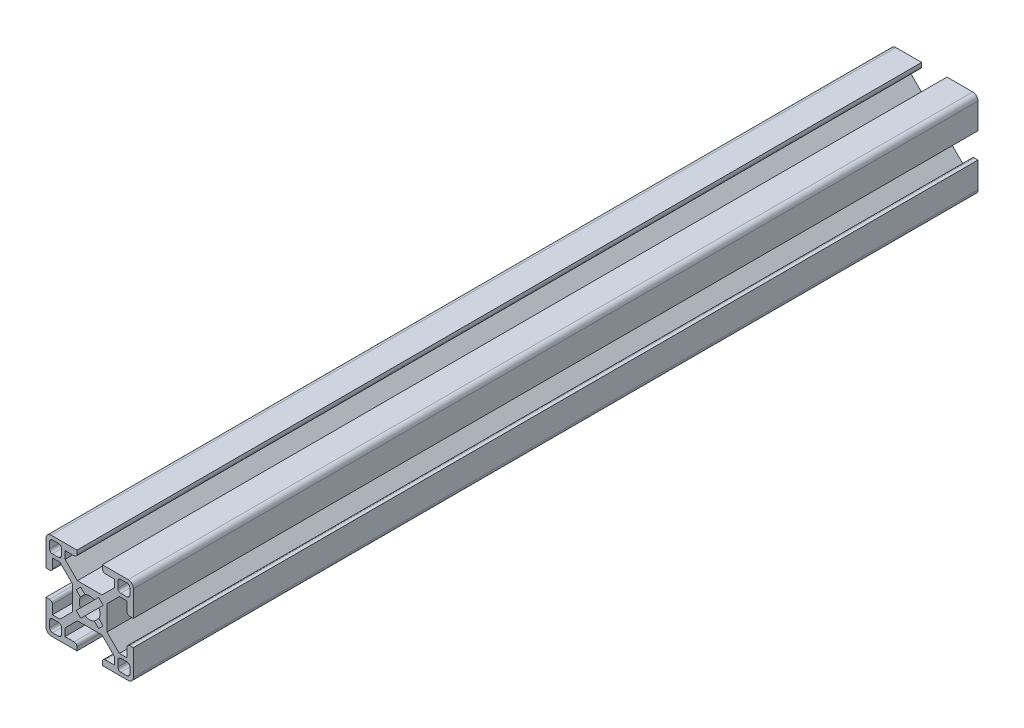
SolidWorks part; units mm, degrees
ref_plane "Front Plane" through (0, 0, 0) normal (0, 0, 1) x (1, 0, 0)
ref_plane "Top Plane" through (0, 0, 0) normal (0, 1, 0) x (1, 0, 0)
ref_plane "Right Plane" through (0, 0, 0) normal (1, 0, 0) x (0, 0, -1)
sketch "Sketch1" plane through (0, 0, 0) normal (0, 0, 1) x (1, 0, 0)
  line L0 (0, 0) -> (5.95, 0) construction
  line L1 (0, 0) -> (0, 5.95) construction
  line L2 (-5.95, 5.95) -> (5.95, 5.95)
  line L3 (5.95, 5.95) -> (5.95, 0)
  line L4 (4.2176, 5.95) -> (8.4602, 10.1926)
  line L5 (5.95, 5.95) -> (8.4425, 8.4425) construction
  line L6 (5.95, 4.2176) -> (10.1926, 8.4602)
  line L7 (8.4602, 12.7926) -> (8.4602, 8.4602)
  line L8 (8.4602, 8.4602) -> (12.7926, 8.4602)
  line L9 (12.7926, 8.4602) -> (12.7926, 5.3502)
  line L10 (13.7926, 4.3502) -> (14.9926, 4.3502)
  line L11 (14.9926, 4.3502) -> (14.9926, 13.1926)
  line L12 (8.4602, 8.4602) -> (14.9926, 14.9926) construction
  line L13 (4.3502, 13.7926) -> (4.3502, 14.9926)
  line L14 (4.3502, 14.9926) -> (13.1926, 14.9926)
  line L15 (5.3502, 12.7926) -> (8.4602, 12.7926)
  line L16 (-9.6602, 9.6602) -> (-13.7926, 13.7926) construction
  line L17 (10.6602, 13.7926) -> (12.7926, 13.7926)
  line L18 (9.6602, 12.7926) -> (9.6602, 10.6602)
  line L19 (10.6602, 9.6602) -> (12.7926, 9.6602)
  line L20 (13.7926, 12.7926) -> (13.7926, 10.6602)
  line L21 (9.6602, 13.7926) -> (13.7926, 9.6602) construction
  line L22 (9.6602, 9.6602) -> (13.7926, 13.7926) construction
  line L23 (-9.6602, 13.7926) -> (-13.7926, 9.6602) construction
  line L24 (-8.4602, 8.4602) -> (-14.9926, 14.9926) construction
  line L25 (-5.95, 5.95) -> (-8.4425, 8.4425) construction
  line L26 (-13.7926, 12.7926) -> (-13.7926, 10.6602)
  line L27 (-10.6602, 9.6602) -> (-12.7926, 9.6602)
  line L28 (-9.6602, 12.7926) -> (-9.6602, 10.6602)
  line L29 (-10.6602, 13.7926) -> (-12.7926, 13.7926)
  line L30 (-5.3502, 12.7926) -> (-8.4602, 12.7926)
  line L31 (-4.3502, 14.9926) -> (-13.1926, 14.9926)
  line L32 (-4.3502, 13.7926) -> (-4.3502, 14.9926)
  line L33 (-14.9926, 4.3502) -> (-14.9926, 13.1926)
  line L34 (-13.7926, 4.3502) -> (-14.9926, 4.3502)
  line L35 (-12.7926, 8.4602) -> (-12.7926, 5.3502)
  line L36 (-8.4602, 8.4602) -> (-12.7926, 8.4602)
  line L37 (-8.4602, 12.7926) -> (-8.4602, 8.4602)
  line L38 (-5.95, 4.2176) -> (-10.1926, 8.4602)
  line L39 (-4.2176, 5.95) -> (-8.4602, 10.1926)
  line L40 (-5.95, 5.95) -> (-5.95, 0)
  line L41 (-5.95, 0) -> (5.95, 0)
  arc A0 (13.1926, 14.9926) -> (14.9926, 13.1926) centre (13.1926, 13.1926) cw
  arc A1 (10.6602, 13.7926) -> (9.6602, 12.7926) centre (10.6602, 12.7926) ccw
  arc A2 (12.7926, 13.7926) -> (13.7926, 12.7926) centre (12.7926, 12.7926) cw
  arc A3 (12.7926, 9.6602) -> (13.7926, 10.6602) centre (12.7926, 10.6602) ccw
  arc A4 (9.6602, 10.6602) -> (10.6602, 9.6602) centre (10.6602, 10.6602) ccw
  arc A5 (4.3502, 13.7926) -> (5.3502, 12.7926) centre (5.3502, 13.7926) ccw
  arc A6 (12.7926, 5.3502) -> (13.7926, 4.3502) centre (13.7926, 5.3502) ccw
  arc A7 (-12.7926, 5.3502) -> (-13.7926, 4.3502) centre (-13.7926, 5.3502) cw
  arc A8 (-4.3502, 13.7926) -> (-5.3502, 12.7926) centre (-5.3502, 13.7926) cw
  arc A9 (-9.6602, 10.6602) -> (-10.6602, 9.6602) centre (-10.6602, 10.6602) cw
  arc A10 (-12.7926, 9.6602) -> (-13.7926, 10.6602) centre (-12.7926, 10.6602) cw
  arc A11 (-12.7926, 13.7926) -> (-13.7926, 12.7926) centre (-12.7926, 12.7926) ccw
  arc A12 (-10.6602, 13.7926) -> (-9.6602, 12.7926) centre (-10.6602, 12.7926) cw
  arc A13 (-13.1926, 14.9926) -> (-14.9926, 13.1926) centre (-13.1926, 13.1926) ccw
  point P12 (11.7264, 11.7264)
  point P40 (4.3502, 12.7926)
  point P43 (12.7926, 4.3502)
  point P82 (-12.7926, 4.3502)
  point P83 (-4.3502, 12.7926)
  point P84 (-11.7264, 11.7264)
  dimension "D9" = 1.8
  dimension "D10" = 1
  dimension "D11" = 1
  dimension "D1" = 5.95
  dimension "D4" = 2.6
  dimension "D2" = 135
  dimension "D3" = 2.45
  dimension "D5" = 6
  dimension "D6" = 4.11
  dimension "D7" = 2.2
  dimension "D8" = 1.2
extrude "Boss-Extrude1" add sketch "Sketch1" against normal blind 290 contours L31 A13 L33 L34 A7 L35 L36 L37 L30 A8 L32 L29 A12 L28 A9 L27 A10 L26 A11 | L40 L2 L39 L37 L36 L38 | L40 L41 L3 L2 | L8 L7 L4 L2 L3 L6 | L9 A6 L10 L11 A0 L14 L13 A5 L15 L7 L8 A4 L18 A1 L17 A2 L20 A3 L19
mirror "Mirror1" about plane through (0, 0, -290) normal (0, -1, 0) of bodies 101
sketch "Sketch2" plane through (0, 0, 0) normal (0, 0, 1) x (1, 0, 0)
  line L0 (-3.0759, -4.6315) -> (4.6315, 3.0759)
  line L1 (-3.0759, -4.6315) -> (-4.6315, -3.0759)
  line L2 (4.6315, 3.0759) -> (3.0759, 4.6315)
  line L3 (-4.6315, -3.0759) -> (3.0759, 4.6315)
  line L4 (-3.0759, -4.6315) -> (3.0759, 4.6315) construction
  line L5 (4.6315, 3.0759) -> (-4.6315, -3.0759) construction
  line L6 (0, 0) -> (0, 2.5254) construction
  line L7 (-4.6315, 3.0759) -> (3.0759, -4.6315)
  line L8 (-4.6315, 3.0759) -> (-3.0759, 4.6315)
  line L9 (-3.0759, 4.6315) -> (4.6315, -3.0759)
  line L10 (3.0759, -4.6315) -> (4.6315, -3.0759)
  line L11 (0, 0) -> (3.0759, 4.6315) construction
  line L12 (0, 0) -> (4.6315, -3.0759) construction
  circle A0 centre (0, 0) radius 3.555
  dimension "D1" = 7.11
  dimension "D2" = 45
  dimension "D3" = 2.2
  dimension "D4" = 10.9
  dimension "D6" = 90
  dimension "D5" = 2
extrude "Cut-Extrude1" cut sketch "Sketch2" against normal through all contours A0 L9 L8 L7 | L9 A0 L7 L3 | L7 A0 L3 | A0 L3 L1 L0 | L3 A0 L0 L7 | L0 A0 L7 | L7 A0 L9 L0 | L9 A0 L0 | L9 L3 L7 L0 | L0 A0 L3 L9 | L3 A0 L9 | A0 L0 L2 L3 | A0 L7 L10 L9
